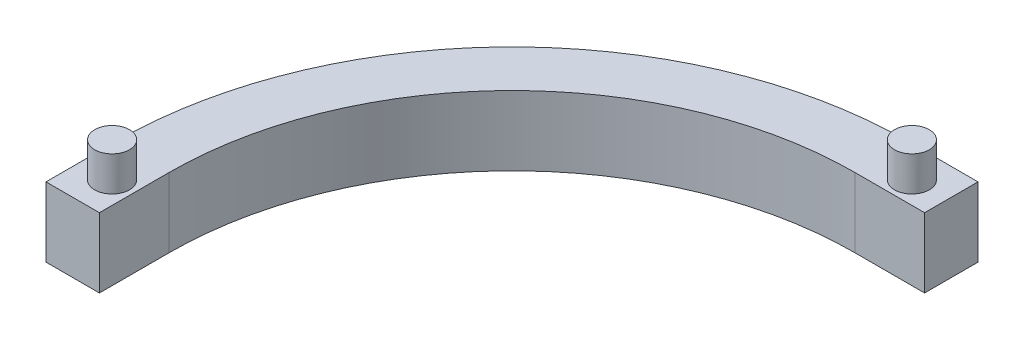
SolidWorks part; units mm, degrees
ref_plane "Front Plane" through (0, 0, 0) normal (0, 0, 1) x (1, 0, 0)
ref_plane "Top Plane" through (0, 0, 0) normal (0, 1, 0) x (1, 0, 0)
ref_plane "Right Plane" through (0, 0, 0) normal (1, 0, 0) x (0, 0, -1)
sketch "Sketch1" plane through (0, 0, 0) normal (0, 1, 0) x (1, 0, 0)
  line L0 (-57, 0) -> (-47.5, 0) construction
  line L1 (47.5, 0) -> (57, 0) construction
  line L2 (-57, 0) -> (-57, -10)
  line L3 (-57, -10) -> (-47.5, -10)
  line L4 (-47.5, -10) -> (-47.5, 0)
  line L5 (47.5, 0) -> (47.5, -10)
  line L6 (47.5, -10) -> (57, -10)
  line L7 (57, -10) -> (57, 0)
  arc A0 (-47.5, 0) -> (47.5, 0) centre (0, 0) cw
  arc A1 (-57, 0) -> (57, 0) centre (0, 0) cw
  dimension "D1" = 57
  dimension "D2" = 47.5
  dimension "D3" = 10
  dimension "D4" = 10
extrude "Boss-Extrude1" add sketch "Sketch1" along normal blind 10
sketch "Sketch2" plane through (0, 0, 0) normal (0, -1, 0) x (1, 0, 0)
  line L0 (-47.5, 10) -> (-47.5, 0) construction
  line L1 (-57, 10) -> (-47.5, 10) construction
  circle A0 centre (-52.5, 5) radius 3
  dimension "D2" = 6
  dimension "D1" = 5
  dimension "D3" = 5
ref_plane "Plane1" through (0, 0, 0) normal (-1, 0, 0) x (0, 0, 1)
sketch "Sketch3" plane through (0, 10, 0) normal (0, 1, 0) x (1, 0, 0)
  circle A0 centre (-52.5, -5) radius 2.5
  dimension "D1" = 5
extrude "Cut-Extrude1" cut sketch "Sketch2" against normal blind 6 contours A0
extrude "Boss-Extrude2" add sketch "Sketch3" along normal blind 5
mirror "Mirror1" about plane through (0, 0, 0) normal (-1, 0, 0) of "Boss-Extrude2", "Cut-Extrude1"
sketch "Sketch4" plane through (0, 10, 0) normal (0, 1, 0) x (1, 0, 0)
  line L0 (0, 47.5) -> (0, 57)
  arc A0 (47.5, 0) -> (-47.5, 0) centre (0, 0) ccw construction
  arc A1 (57, 0) -> (-57, 0) centre (0, 0) ccw construction
split "Split1" trim tools "Sketch4" bodies to split 104 resulting bodies 105
sketch "Sketch5" plane through (0, 0, 0) normal (1, 0, 0) x (0, 0, -1)
  line L1 (47.5, 10) -> (57, 10)
  line L2 (47.5, 10) -> (47.5, 0)
  line L3 (47.5, 0) -> (57, 0)
  line L4 (57, 10) -> (57, 0)
extrude "Boss-Extrude3" add sketch "Sketch5" along normal blind 10
sketch "Sketch6" plane through (0, 10, 0) normal (0, 1, 0) x (1, 0, 0)
  line L0 (10, 47.5) -> (0, 47.5) construction
  line L1 (10, 57) -> (10, 47.5) construction
  circle A0 centre (5, 52.5) radius 2.5
  dimension "D1" = 5
  dimension "D2" = 5
  dimension "D3" = 5
extrude "Boss-Extrude4" add sketch "Sketch6" along normal blind 5
sketch "Sketch7" plane through (0, 0, 0) normal (0, -1, 0) x (1, 0, 0)
  line L0 (10, -47.5) -> (0, -47.5) construction
  line L1 (10, -47.5) -> (10, -57) construction
  circle A0 centre (5, -52.5) radius 3
  dimension "D1" = 6
  dimension "D2" = 5
  dimension "D3" = 5
extrude "Cut-Extrude2" cut sketch "Sketch7" against normal blind 5
sketch "Sketch9" plane through (0, 10, 0) normal (0, 1, 0) x (1, 0, 0)
  line L0 (0, 47.5) -> (0, 57) construction
  line L1 (-49.32, 0) -> (-49.32, -10)
  line L2 (-57, -10) -> (-47.5, -10) construction
  line L3 (0, 49.32) -> (10, 49.32)
  line L4 (10, 57) -> (10, 47.5) construction
  arc A0 (0, 49.32) -> (-49.32, 0) centre (0, 0) ccw
  dimension "D1" = 49.32
split "Split3" trim tools "Sketch9" bodies to split 108 resulting bodies 110
